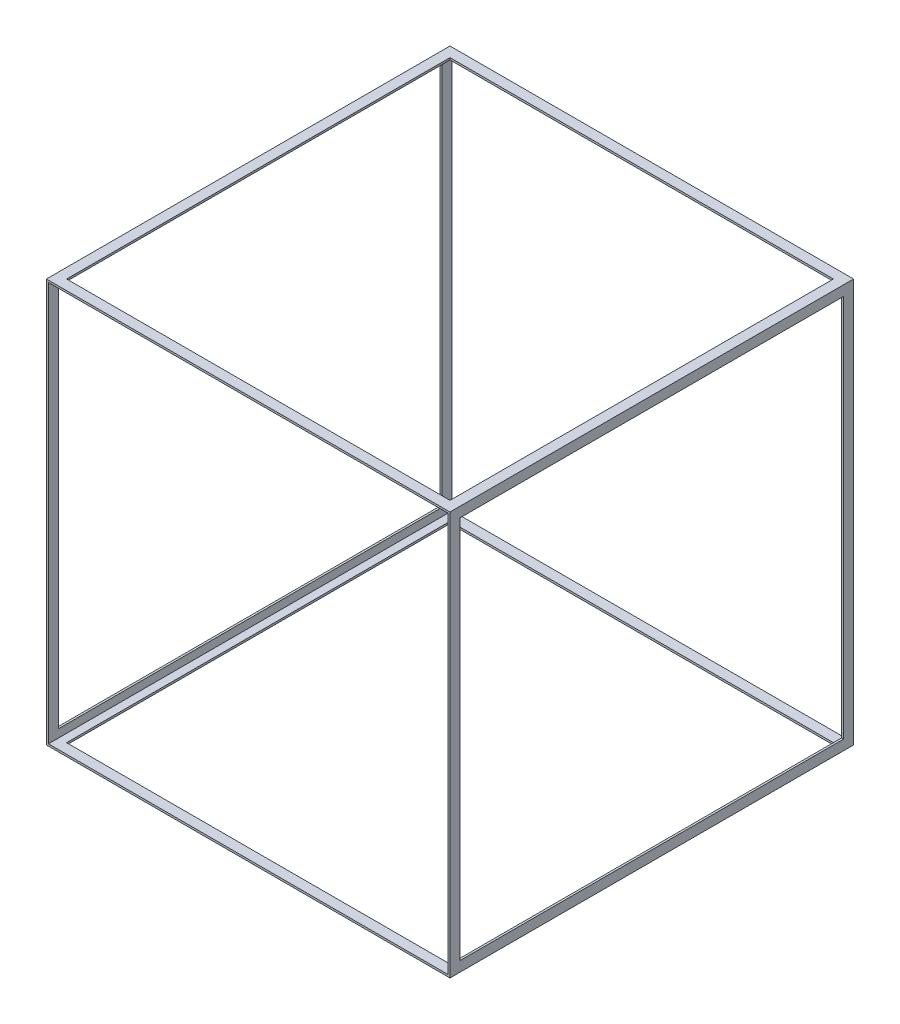
SolidWorks part; units mm, degrees
ref_plane "Front Plane" through (0, 0, 0) normal (0, 0, 1) x (1, 0, 0)
ref_plane "Top Plane" through (0, 0, 0) normal (0, 1, 0) x (1, 0, 0)
ref_plane "Right Plane" through (0, 0, 0) normal (1, 0, 0) x (0, 0, -1)
sketch "Sketch3" plane through (0, 0, 0) normal (0, 0, 1) x (1, 0, 0)
  line L0 (100, 100) -> (100, 19900)
  line L1 (0, 0) -> (20000, 0)
  line L2 (0, 0) -> (0, 20000)
  line L3 (0, 20000) -> (20000, 20000)
  line L4 (20000, 0) -> (20000, 20000)
  line L5 (100, 19900) -> (19900, 19900)
  line L6 (19900, 100) -> (19900, 19900)
  line L7 (100, 100) -> (19900, 100)
  dimension "D1" = 20000
  dimension "D2" = 20000
  dimension "D3" = 100
extrude "Boss-Extrude1" add sketch "Sketch3" along normal blind 20000
sketch "Sketch4" plane through (0, 0, 0) normal (-1, 0, 0) x (0, 0, 1)
  line L0 (20000, 20000) -> (0, 20000) construction
  line L1 (19500, 19500) -> (500, 19500)
  line L2 (19500, 19500) -> (19500, 500)
  line L3 (19500, 500) -> (500, 500)
  line L4 (500, 19500) -> (500, 500)
  line L5 (20000, 0) -> (0, 0) construction
  line L6 (20000, 20000) -> (20000, 0) construction
  line L7 (0, 20000) -> (0, 0) construction
  dimension "D1" = 500
  dimension "D2" = 500
  dimension "D3" = 500
  dimension "D4" = 500
extrude "Cut-Extrude1" cut sketch "Sketch4" against normal through all both and the other way through all
sketch "Sketch5" plane through (0, 0, 0) normal (0, -1, 0) x (1, 0, 0)
  line L0 (0, 20000) -> (0, 0) construction
  line L1 (500, 19500) -> (19500, 19500)
  line L2 (500, 19500) -> (500, 500)
  line L3 (500, 500) -> (19500, 500)
  line L4 (19500, 19500) -> (19500, 500)
  line L5 (20000, 20000) -> (20000, 0) construction
  line L6 (0, 0) -> (20000, 0) construction
  line L7 (0, 20000) -> (20000, 20000) construction
  dimension "D1" = 500
  dimension "D2" = 500
  dimension "D3" = 500
  dimension "D4" = 500
extrude "Cut-Extrude2" cut sketch "Sketch5" against normal blind 20000
